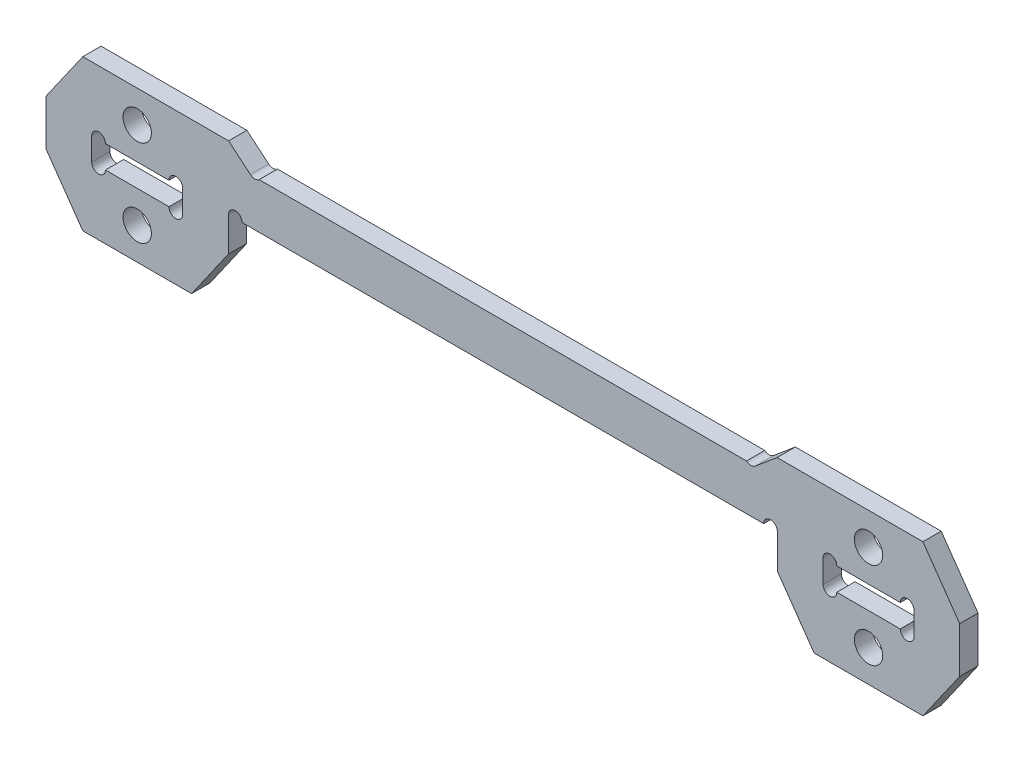
SolidWorks part; units mm, degrees
ref_plane "前视基准面" through (0, 0, 0) normal (0, 0, 1) x (1, 0, 0)
ref_plane "上视基准面" through (0, 0, 0) normal (0, 1, 0) x (1, 0, 0)
ref_plane "右视基准面" through (0, 0, 0) normal (1, 0, 0) x (0, 0, -1)
sketch "草图1" plane through (0, 0, 0) normal (0, 0, 1) x (1, 0, 0)
  line L0 (0, -4.75) -> (0, 4.75) construction
  line L1 (-35.025, -1.25) -> (-44.975, -1.25)
  line L2 (-35.025, -1.25) -> (-35.025, 1.25)
  line L3 (-35.025, 1.25) -> (-44.975, 1.25)
  line L4 (-44.975, -1.25) -> (-44.975, 1.25)
  line L5 (-35.025, -1.25) -> (-44.975, 1.25) construction
  line L6 (-35.025, 1.25) -> (-44.975, -1.25) construction
  line L7 (35.025, 1.25) -> (44.975, 1.25)
  line L8 (44.975, -1.25) -> (44.975, 1.25)
  line L9 (35.025, -1.25) -> (44.975, -1.25)
  line L10 (35.025, -1.25) -> (35.025, 1.25)
  line L11 (-30.025, 1.25) -> (-30.025, -2.5)
  line L12 (-30.025, -2.5) -> (-34.0512, -8.25)
  line L13 (-34.0512, -8.25) -> (-45.9488, -8.25)
  line L14 (-45.9488, -8.25) -> (-49.975, -2.5)
  line L15 (-49.975, -2.5) -> (-49.975, 2.5)
  line L16 (-49.975, 2.5) -> (-45.9488, 8.25)
  line L17 (-45.9488, 8.25) -> (45.9488, 8.25)
  line L18 (-30.025, 1.25) -> (30.025, 1.25)
  line L19 (30.025, 1.25) -> (30.025, -2.5)
  line L20 (30.025, -2.5) -> (34.0512, -8.25)
  line L21 (34.0512, -8.25) -> (45.9488, -8.25)
  line L22 (45.9488, -8.25) -> (49.975, -2.5)
  line L23 (49.975, -2.5) -> (49.975, 2.5)
  line L24 (49.975, 2.5) -> (45.9488, 8.25)
  circle A0 centre (-40, 4.75) radius 1.55
  circle A1 centre (-40, -4.75) radius 1.55
  circle A2 centre (40, -4.75) radius 1.55
  circle A3 centre (40, 4.75) radius 1.55
  point P4 (-40, 0)
  point P13 (0, 0)
  point P33 (-49.975, 0)
  point P43 (0, 8.25)
  point P44 (0, 1.25)
  dimension "D1" = 3.1
  dimension "D5" = 3.5
  dimension "D7" = 3.5
  dimension "D2" = 2.5
  dimension "D3" = 9.95
  dimension "D4" = 80
  dimension "D6" = 5
  dimension "D8" = 5
  dimension "D9" = 55
  dimension "D10" = 5
extrude "凸台-拉伸1" add sketch "草图1" along normal mid plane 2
sketch "草图2" plane through (0, 0, 1) normal (0, 0, 1) x (1, 0, 0)
  line L0 (-35.025, 1.25) -> (-44.975, 1.25) construction
  line L1 (-44.975, -1.25) -> (-35.025, -1.25) construction
  line L2 (-30.025, 1.25) -> (30.025, 1.25) construction
  line L3 (0, 1.25) -> (0, 8.25) construction
  line L4 (45.9488, 8.25) -> (-45.9488, 8.25) construction
  circle A0 centre (-35.775, 1.25) radius 0.75
  circle A1 centre (-35.775, -1.25) radius 0.75
  circle A2 centre (-44.225, 1.25) radius 0.75
  circle A3 centre (-44.225, -1.25) radius 0.75
  circle A4 centre (-29.275, 1.25) radius 0.75
  circle A5 centre (29.275, 1.25) radius 0.75
  circle A6 centre (44.225, -1.25) radius 0.75
  circle A7 centre (44.225, 1.25) radius 0.75
  circle A8 centre (35.775, -1.25) radius 0.75
  circle A9 centre (35.775, 1.25) radius 0.75
  dimension "D1" = 1.5
extrude "切除-拉伸1" cut sketch "草图2" against normal through all
sketch "草图3" plane through (0, 0, 1) normal (0, 0, 1) x (1, 0, 0)
  line L0 (-30, 8.25) -> (-27.6165, 6.25)
  line L1 (45.9488, 8.25) -> (-45.9488, 8.25) construction
  line L2 (-27.6165, 6.25) -> (27.6165, 6.25)
  line L3 (0, 6.25) -> (0, 8.25) construction
  line L4 (30, 8.25) -> (-30, 8.25)
  line L5 (-28.525, 1.25) -> (28.525, 1.25) construction
  line L6 (30, 8.25) -> (27.6165, 6.25)
  dimension "D1" = 5
  dimension "D2" = 40
  dimension "D3" = 30
extrude "切除-拉伸2" cut sketch "草图3" against normal through all
sketch "草图4" plane through (0, 0, 1) normal (0, 0, 1) x (1, 0, 0)
  line L0 (-30, 8.25) -> (-27.6165, 6.25) construction
  line L1 (27.6165, 6.25) -> (30, 8.25) construction
  circle A0 centre (-27.1344, 6.8245) radius 0.75
  circle A1 centre (27.1344, 6.8245) radius 0.75
  arc A2 (-28.525, 1.25) -> (-30.025, 1.25) centre (-29.275, 1.25) ccw construction
extrude "切除-拉伸3" cut sketch "草图4" against normal through all
